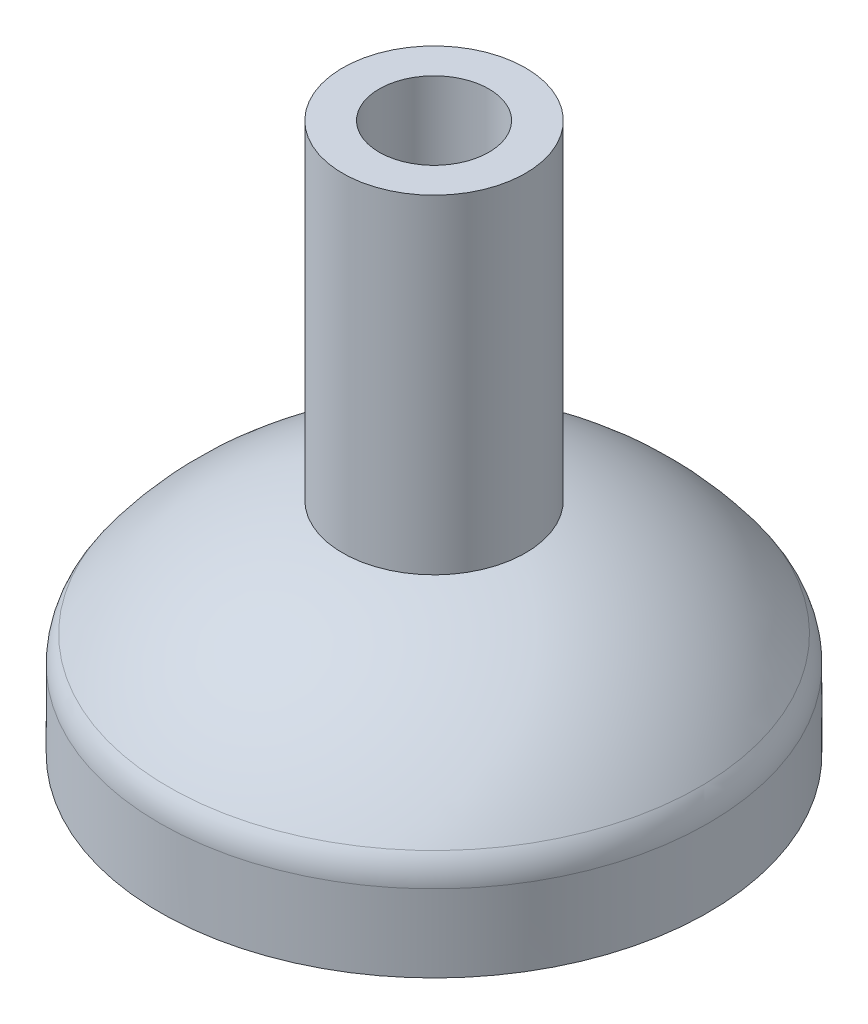
SolidWorks part; units mm, degrees
ref_plane "Ebene vorne" through (0, 0, 0) normal (0, 0, 1) x (1, 0, 0)
ref_plane "Ebene oben" through (0, 0, 0) normal (0, 1, 0) x (1, 0, 0)
ref_plane "Ebene rechts" through (0, 0, 0) normal (1, 0, 0) x (0, 0, -1)
sketch "Skizze2" plane through (0, 0, 0) normal (0, 0, 1) x (1, 0, 0)
  line L0 (0, 14.0407) -> (0, 50)
  line L1 (0, 14.0407) -> (0, 9.1763)
  line L2 (-10, 14.0407) -> (-10, 50)
  line L3 (0, 9.1763) -> (-8.8434, 9.1763)
  line L4 (-30, 0) -> (-30, -10)
  line L5 (-25.8178, -2.7403) -> (-25.8178, -10)
  line L6 (-25.8178, -10) -> (-30, -10)
  line L7 (-10, 50) -> (0, 50)
  arc A0 (-30, 0) -> (-10, 14.0407) centre (-2.3549, -18.1138) cw
  arc A1 (-25.8178, -2.7403) -> (-8.8434, 9.1763) centre (-2.3549, -18.1138) cw
  dimension "D2" = 5
  dimension "D3" = 10
  dimension "D1" = 10
revolve "Rotation2" add sketch "Skizze2" angle 360 about L0
sketch "Skizze4" plane through (0, 0, 0) normal (0, 1, 0) x (1, 0, 0)
  circle A0 centre (0, 0) radius 6
extrude "Schnitt-Linear austragen2" cut sketch "Skizze4" along normal through all contours A0
fillet "Verrundung2" radius 5 1 edges at (0, 0, -30)
other "Trennfuge3"
other "Trennoberfläche7" parameters "D1"=20
